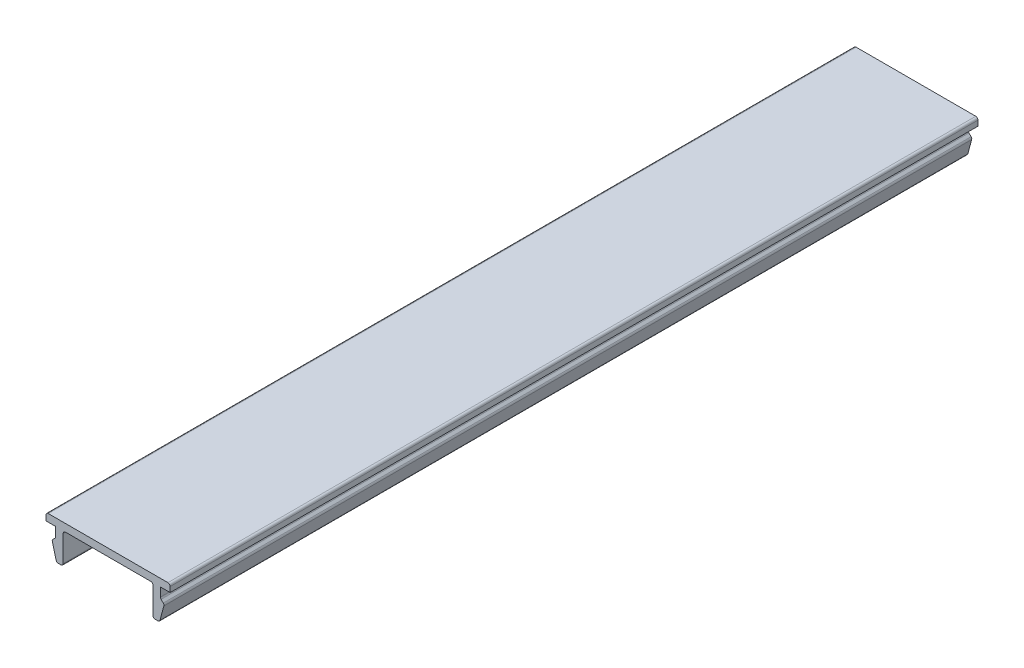
SolidWorks part; units mm, degrees
material "ABS"
ref_plane "Plano frontal" through (0, 0, 0) normal (0, 0, 1) x (1, 0, 0)
ref_plane "Plano superior" through (0, 0, 0) normal (0, 1, 0) x (1, 0, 0)
ref_plane "Plano direito" through (0, 0, 0) normal (1, 0, 0) x (0, 0, -1)
sketch "Sketch1" plane through (0, 0, 0) normal (0, 0, 1) x (1, 0, 0)
  line L0 (-8.3, 1) -> (8.3, 1)
  line L1 (-8.3, 0) -> (-7, 0)
  line L2 (-8.3, 1) -> (-8.3, 0)
  line L3 (8.3, 1) -> (8.3, 0)
  line L4 (-7, 0) -> (-7, -1.3)
  line L5 (-7, -1.3) -> (-7.5, -1.8)
  line L6 (-7.5, -1.8) -> (-6.8837, -4.1)
  line L7 (-6, 0) -> (-6, -4.1)
  line L8 (-6, -4.1) -> (-6.8837, -4.1)
  line L9 (0, 0) -> (0, -1.7195) construction
  line L10 (6, -4.1) -> (6.8837, -4.1)
  line L11 (6, 0) -> (6, -4.1)
  line L12 (7.5, -1.8) -> (6.8837, -4.1)
  line L13 (7, -1.3) -> (7.5, -1.8)
  line L14 (7, 0) -> (7, -1.3)
  line L15 (7, 0) -> (8.3, 0)
  line L16 (-8.3, 0) -> (8.3, 0) construction
  line L17 (-6, 0) -> (6, 0)
  point P21 (0, 1)
  dimension "D1" = 16.6
  dimension "D3" = 1.3
  dimension "D4" = 1.3
  dimension "D5" = 135
  dimension "D6" = 120
  dimension "D7" = 4.1
  dimension "D8" = 0.5
  dimension "D9" = 1
  dimension "D2" = 1
extrude "Boss-Extrude1" add sketch "Sketch1" along normal blind 108
fillet "Fillet1" radius 0.3 12 edges at (8.3, 1, 54) (7, -1.3, 54) (7.5, -1.8, 54) (6.8837, -4.1, 54) (6, -4.1, 54) (6, 0, 54) (-6, 0, 54) (-6, -4.1, 54) (-6.8837, -4.1, 54) (-7.5, -1.8, 54) (-7, -1.3, 54) (-8.3, 1, 54)
